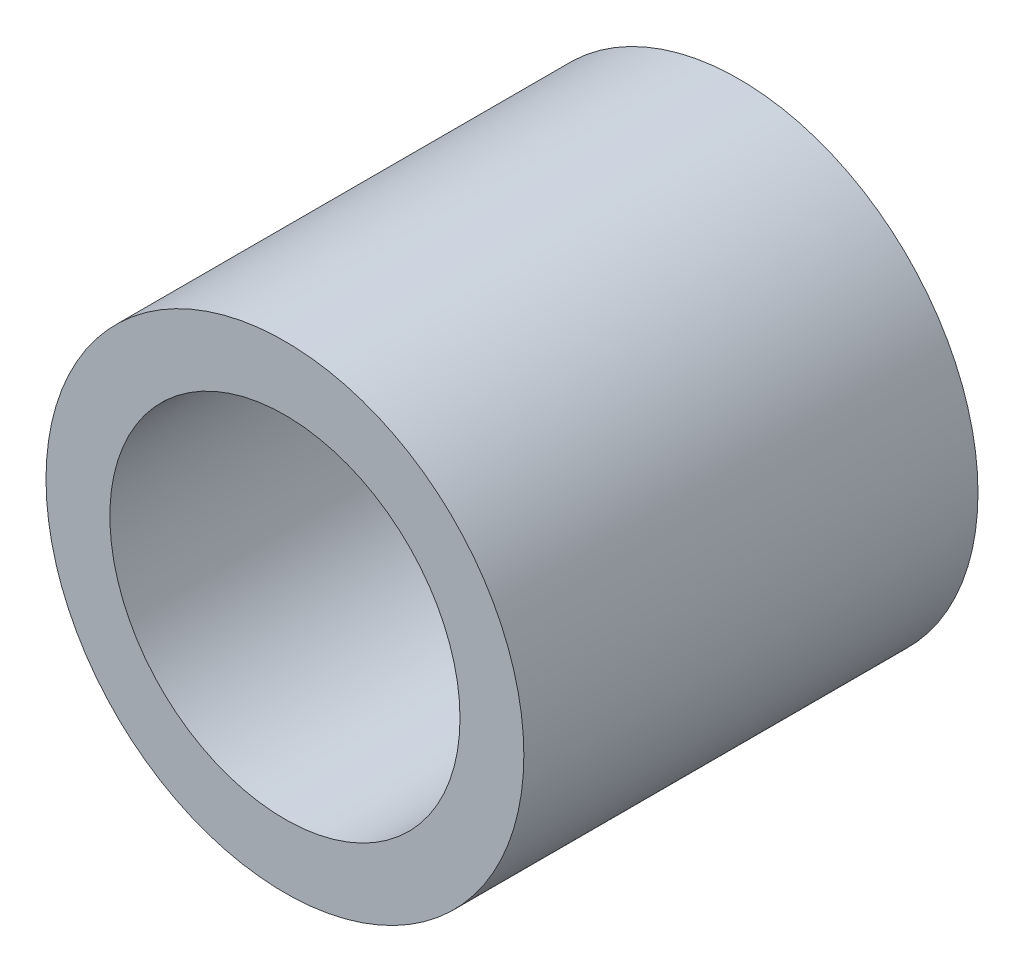
SolidWorks part; units mm, degrees
material "PVC 0.007 Plasticized"
ref_plane "Front Plane" through (0, 0, 0) normal (0, 0, 1) x (1, 0, 0)
ref_plane "Top Plane" through (0, 0, 0) normal (0, 1, 0) x (1, 0, 0)
ref_plane "Right Plane" through (0, 0, 0) normal (1, 0, 0) x (0, 0, -1)
sketch "Sketch1" plane through (0, 0, 0) normal (0, 0, 1) x (1, 0, 0)
  circle A1 centre (0, 0) radius 4.6101
  dimension "D1" = 9.2202
extrude "Boss-Extrude1" add sketch "Sketch1" against normal blind 8.763
hole_wizard "H (0.266) Diameter Hole1" positions "Sketch2" profile "Sketch3" hole size "H" standard "ANSI Inch" end condition through all
sketch "Sketch2" plane through (0, 0, 0) normal (0, 0, 1) x (1, 0, 0)
  point P0 (0, 0)
sketch "Sketch3" plane through (0, 0, 0) normal (1, 0, 0) x (0, -1, 0)
  line L0 (0, 0) -> (0, 8.763)
  line L1 (0, 8.763) -> (3.3782, 8.763)
  line L2 (3.3782, 8.763) -> (3.3782, 0)
  line L5 (3.3782, 0) -> (0, 0)
  line L11 (0, -6.35) -> (0, 107.95) construction
  dimension "Thru Hole Dia." = 6.7564
  dimension "Thru Hole Depth" = 8.763
